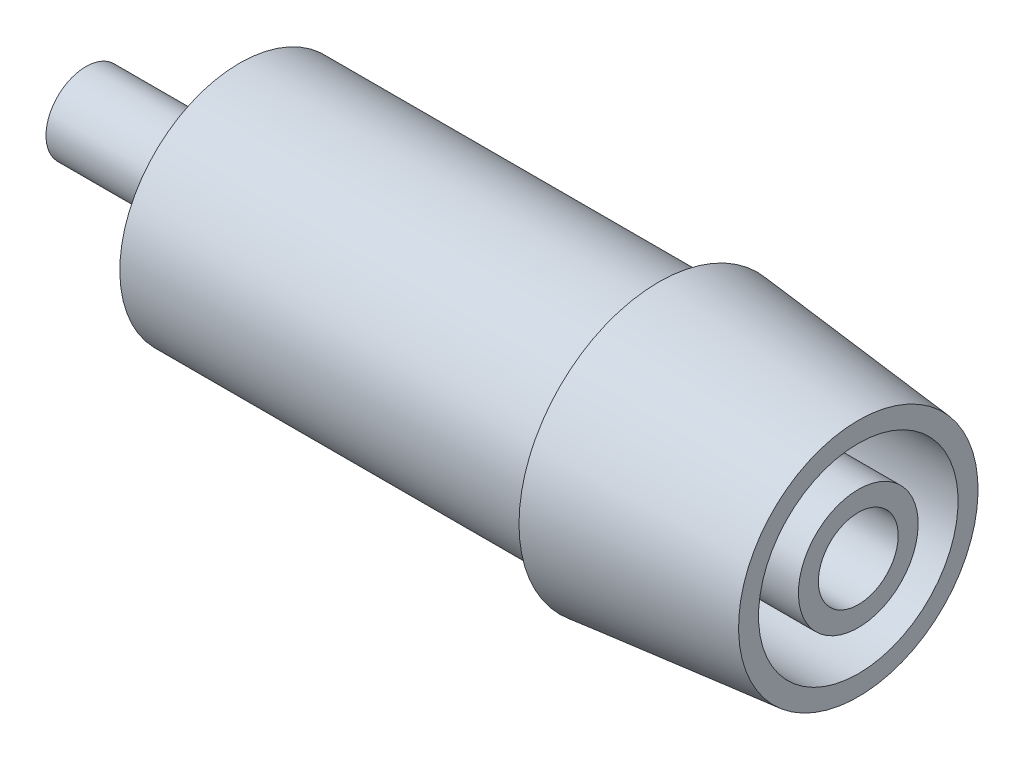
SolidWorks part; units mm, degrees
ref_plane "Płaszczyzna przednia" through (0, 0, 0) normal (0, 0, 1) x (1, 0, 0)
ref_plane "Płaszczyzna górna" through (0, 0, 0) normal (0, 1, 0) x (1, 0, 0)
ref_plane "Płaszczyzna prawa" through (0, 0, 0) normal (1, 0, 0) x (0, 0, -1)
sketch "Szkic1" plane through (0, 0, 0) normal (0, 0, 1) x (1, 0, 0)
  line L0 (0, 0) -> (0, 2)
  line L1 (0, 2) -> (7.7, 2)
  line L4 (7.7, 2) -> (7.7, 6)
  line L5 (7.7, 6) -> (28.7, 6)
  line L6 (28.7, 6) -> (28.7, 7)
  line L7 (28.7, 7) -> (38.7, 6)
  line L8 (38.7, 6) -> (38.7, 5)
  line L9 (38.7, 5) -> (16.7, 5)
  line L10 (16.7, 5) -> (16.7, 3)
  line L11 (16.7, 3) -> (38.7, 3)
  line L12 (38.7, 3) -> (38.7, 2)
  line L13 (38.7, 2) -> (16.7, 2)
  line L14 (16.7, 2) -> (16.7, 0)
  line L15 (16.7, 0) -> (0, 0)
  dimension "D1" = 2
  dimension "D2" = 2
  dimension "D3" = 1
  dimension "D4" = 2
  dimension "D5" = 6
  dimension "D6" = 10
  dimension "D7" = 22
  dimension "D8" = 38.7
  dimension "D9" = 1
  dimension "D10" = 31
  dimension "D11" = 7
revolve "Obrót1" add sketch "Szkic1" angle 360 about L15
